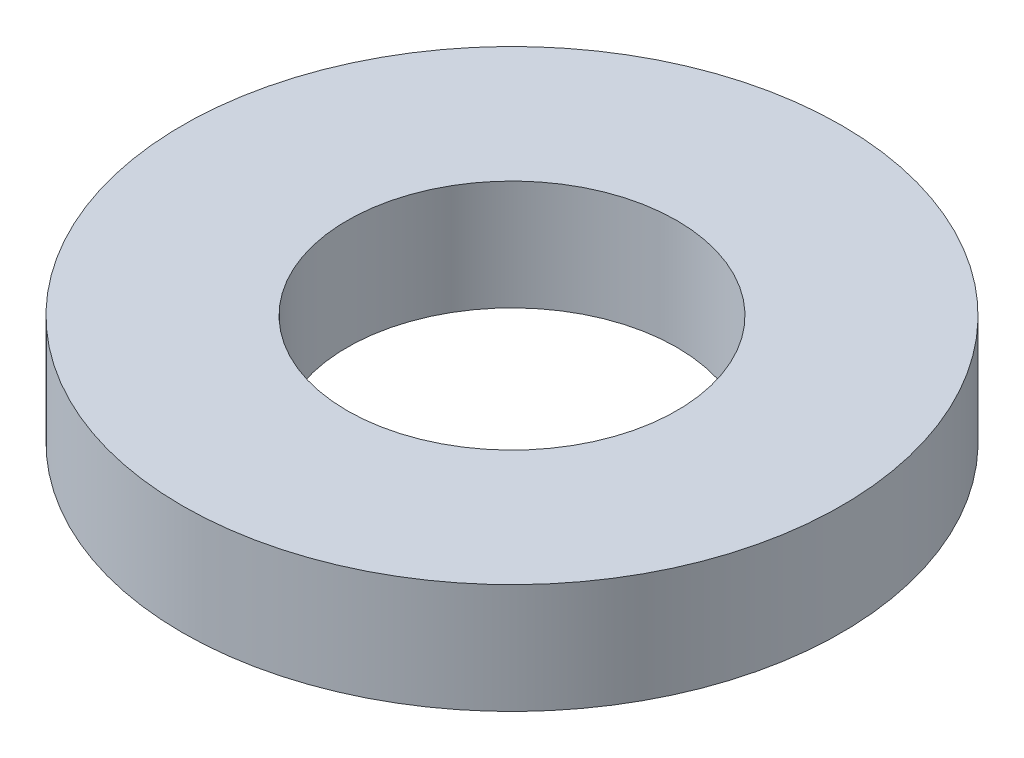
SolidWorks part; units mm, degrees
ref_plane "前视基准面" through (0, 0, 0) normal (0, 0, 1) x (1, 0, 0)
ref_plane "上视基准面" through (0, 0, 0) normal (0, 1, 0) x (1, 0, 0)
ref_plane "右视基准面" through (0, 0, 0) normal (1, 0, 0) x (0, 0, -1)
sketch "草图1" plane through (0, 0, 0) normal (0, 1, 0) x (1, 0, 0)
  circle A0 centre (0, 0) radius 3
  circle A1 centre (0, 0) radius 1.5
  dimension "D1" = 3
  dimension "D2" = 6
extrude "凸台-拉伸1" add sketch "草图1" along normal blind 1
